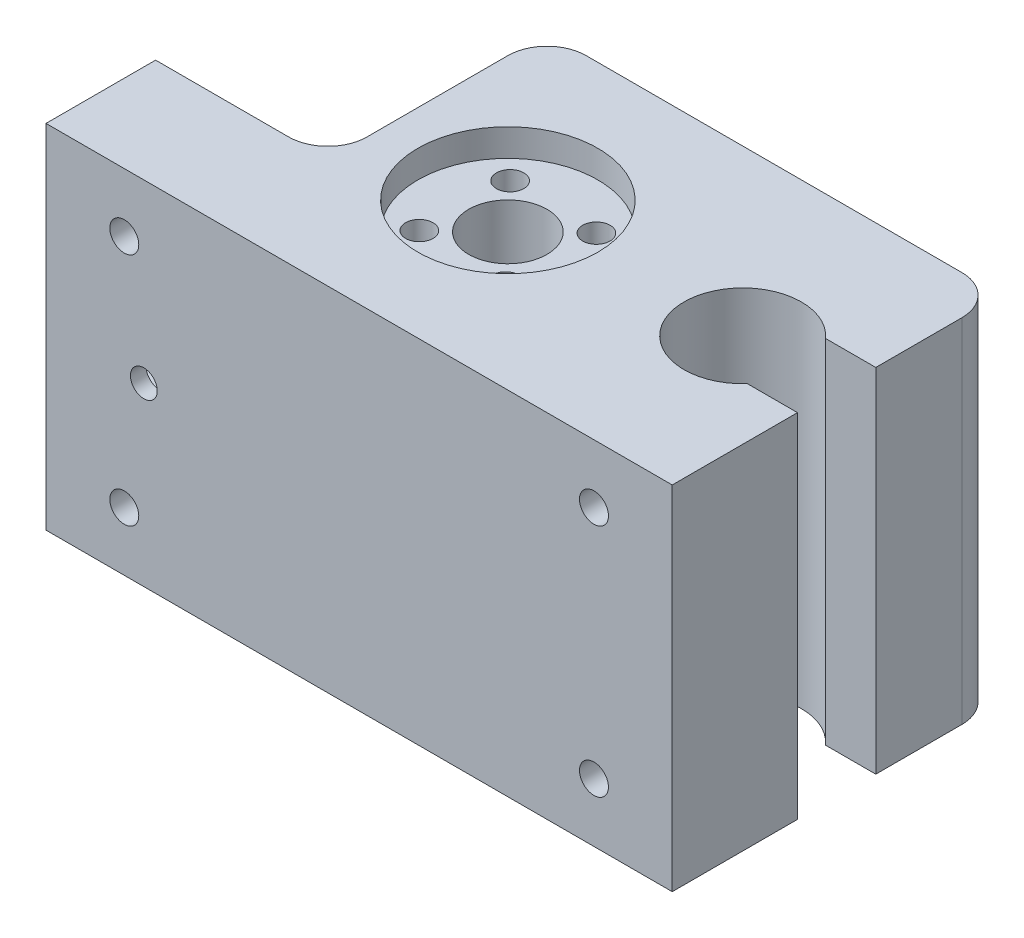
SolidWorks part; units mm, degrees
ref_plane "Front Plane" through (0, 0, 0) normal (0, 0, 1) x (1, 0, 0)
ref_plane "Top Plane" through (0, 0, 0) normal (0, 1, 0) x (1, 0, 0)
ref_plane "Right Plane" through (0, 0, 0) normal (1, 0, 0) x (0, 0, -1)
sketch "Sketch1" plane through (0, 0, 0) normal (0, 0, 1) x (1, 0, 0)
  line L0 (80, 22.5) -> (0, 22.5) construction
  line L1 (0, 0) -> (80, 0)
  line L2 (0, 0) -> (0, 45)
  line L3 (0, 45) -> (80, 45)
  line L4 (80, 0) -> (80, 45)
  dimension "D1" = 80
  dimension "D2" = 45
extrude "Boss-Extrude1" add sketch "Sketch1" along normal blind 42
sketch "Sketch3" plane through (0, 45, 0) normal (0, 1, 0) x (1, 0, 0)
  line L0 (0, -28) -> (22, -28)
  line L1 (0, -42) -> (0, 0) construction
  line L2 (22, -28) -> (22, 0)
  line L3 (80, 0) -> (0, 0) construction
  line L4 (22, 0) -> (0, 0)
  line L5 (0, 0) -> (0, -28)
  dimension "D1" = 28
  dimension "D2" = 22
extrude "Cut-Extrude2" cut sketch "Sketch3" against normal through all
sketch "Sketch4" plane through (0, 0, 0) normal (-1, 0, 0) x (0, 0, 1)
  line L0 (42, 45) -> (42, 0) construction
  line L1 (30, 31) -> (40, 31)
  line L2 (30, 31) -> (30, 14)
  line L3 (30, 14) -> (40, 14)
  line L4 (40, 31) -> (40, 14)
  line L5 (28, 0) -> (28, 45) construction
  line L6 (42, 45) -> (28, 45) construction
  dimension "D1" = 17
  dimension "D2" = 2
  dimension "D3" = 2
  dimension "D4" = 14
extrude "Cut-Extrude3" cut sketch "Sketch4" against normal blind 28
sketch "Sketch7" plane through (0, 45, 0) normal (0, 1, 0) x (1, 0, 0)
  circle A0 centre (38, -21) radius 11.5
extrude "Cut-Extrude5" cut sketch "Sketch7" against normal blind 3.5 contours A0
sketch "Sketch11" plane through (0, 41.5, 0) normal (0, 1, 0) x (1, 0, 0)
  circle A0 centre (32.2016, -26.5117) radius 1.75
  circle A1 centre (32.4883, -15.2016) radius 1.75
  circle A2 centre (43.7984, -15.4883) radius 1.75
  circle A3 centre (43.5117, -26.7984) radius 1.75
extrude "Cut-Extrude6" cut sketch "Sketch11" against normal blind 10
sketch "Sketch12" plane through (0, 41.5, 0) normal (0, 1, 0) x (1, 0, 0)
  circle A0 centre (38, -21) radius 5
extrude "Cut-Extrude7" cut sketch "Sketch12" against normal through all contours A0
sketch "Sketch13" plane through (0, 45, 0) normal (0, 1, 0) x (1, 0, 0)
  circle A0 centre (68, -21) radius 7.5
  dimension "D1" = 15
extrude "Cut-Extrude8" cut sketch "Sketch13" against normal through all
sketch "Sketch14" plane through (0, 45, 0) normal (0, 1, 0) x (1, 0, 0)
  line L0 (68, -21) -> (80, -21) construction
  line L1 (80, -42) -> (80, 0) construction
  line L3 (67.9005, -26) -> (80, -26)
  line L4 (67.9005, -26) -> (67.9005, -16)
  line L5 (67.9005, -16) -> (80, -16)
  line L6 (80, -26) -> (80, -16)
  line L7 (67.9005, -26) -> (80, -16) construction
  line L8 (67.9005, -16) -> (80, -26) construction
  point P5 (73.9502, -21)
  dimension "D1" = 10
extrude "Cut-Extrude9" cut sketch "Sketch14" against normal through all
sketch "Sketch15" plane through (0, 0, 42) normal (0, 0, 1) x (1, 0, 0)
  circle A0 centre (12.5, 22.5) radius 1.7123
extrude "Cut-Extrude10" cut sketch "Sketch15" against normal through all
sketch "Sketch16" plane through (0, 0, 42) normal (0, 0, 1) x (1, 0, 0)
  line L0 (80, 22.5) -> (0, 22.5) construction
  line L1 (80, 0) -> (80, 45) construction
  line L2 (0, 45) -> (0, 0) construction
  line L4 (70, 7.5) -> (10, 7.5) construction
  line L5 (70, 7.5) -> (70, 37.5) construction
  line L6 (70, 37.5) -> (10, 37.5) construction
  line L7 (10, 7.5) -> (10, 37.5) construction
  line L8 (70, 7.5) -> (10, 37.5) construction
  line L9 (70, 37.5) -> (10, 7.5) construction
  circle A0 centre (10, 37.5) radius 1.85
  circle A1 centre (70, 37.5) radius 1.85
  circle A2 centre (70, 7.5) radius 1.85
  circle A3 centre (10, 7.5) radius 1.85
  point P6 (40, 22.5)
  dimension "D3" = 3.7
  dimension "D4" = 3.7
  dimension "D5" = 3.7
  dimension "D6" = 3.7
  dimension "D1" = 30
  dimension "D2" = 60
extrude "Cut-Extrude11" cut sketch "Sketch16" against normal blind 8
fillet "Fillet2" radius 5 3 edges at (22, 22.5, 28) (22, 22.5, 0) (80, 22.5, 0)
